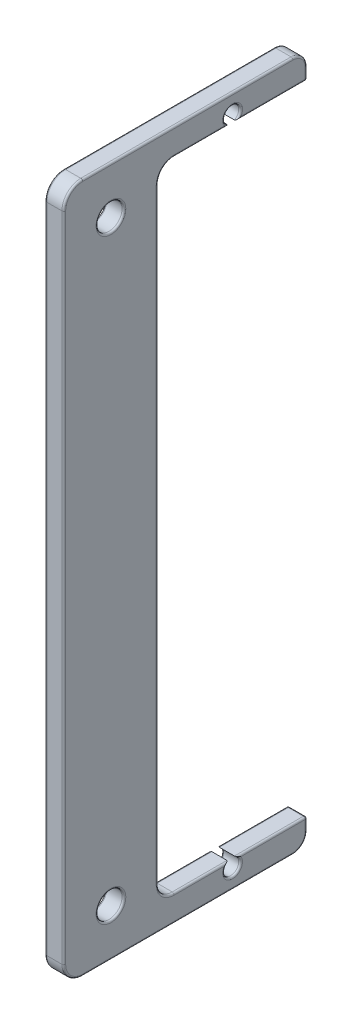
SolidWorks part; units mm, degrees
ref_plane "Front Plane" through (0, 0, 0) normal (0, 0, 1) x (1, 0, 0)
ref_plane "Top Plane" through (0, 0, 0) normal (0, 1, 0) x (1, 0, 0)
ref_plane "Right Plane" through (0, 0, 0) normal (1, 0, 0) x (0, 0, -1)
ref_plane "Plane1" through (102.035, 0, 0) normal (-1, 0, 0) x (0, -1, 0)
sketch "Sketch1" plane through (102.035, 0, 0) normal (-1, 0, 0) x (0, -1, 0)
  line L0 (-127.6, 102.4783) -> (7.6, 102.4783)
  line L2 (13.2, 122.4783) -> (-133.2, 122.4783)
  line L3 (-133.2, 122.4783) -> (-133.2, 70.8783)
  line L4 (-133.2, 70.8783) -> (-127.6, 70.8783)
  line L5 (-127.6, 70.8783) -> (-127.6, 102.4783)
  line L8 (13.2, 122.4783) -> (13.2, 70.8783)
  line L9 (13.2, 70.8783) -> (7.6, 70.8783)
  line L10 (7.6, 70.8783) -> (7.6, 102.4783)
  dimension "D1" = 5.6
  dimension "D2" = 5.6
  dimension "D3" = 51.6
  dimension "D4" = 20
  dimension "D7" = 146.4
extrude "Boss-Extrude1" add sketch "Sketch1" against normal blind 4
ref_plane "Plane2" through (0, 0, 86.4786) normal (0, 0, -1) x (-1, 0, 0)
sketch "Sketch6" plane through (106.035, 0, 0) normal (1, 0, 0) x (0, 0, -1)
  line L0 (-122.4783, 133.2) -> (-70.8783, 133.2) construction
  line L1 (-122.4783, -13.2) -> (-122.4783, 133.2) construction
  line L2 (-70.8783, 133.2) -> (-70.8783, 127.6) construction
  line L3 (-70.8783, -13.2) -> (-122.4783, -13.2) construction
  line L4 (-70.8783, -7.6) -> (-70.8783, -13.2) construction
  circle A0 centre (-86.6783, 129.1) radius 1.7
  circle A1 centre (-112.4783, 123.2) radius 2.75
  circle A2 centre (-112.4783, -3.2) radius 2.75
  circle A3 centre (-86.6783, -9.1) radius 1.7
  dimension "D1" = 3.4
  dimension "D2" = 5.5
  dimension "D3" = 10
  dimension "D5" = 15.8
  dimension "D6" = 4.1
  dimension "D7" = 4.1
  dimension "D8" = 15.8
  dimension "D9" = 10
  dimension "D10" = 10
  dimension "D4" = 10
extrude "Holes" cut sketch "Sketch6" against normal through all
fillet "Fillet1" radius 0.4 6 edges at (104.035, 127.6, 70.8783) (104.035, -7.6, 70.8783) (102.035, 123.2, 109.7283) (102.035, -3.2, 109.7283) (106.035, -3.2, 109.7283) (106.035, 123.2, 109.7283)
fillet "Fillet3" radius 3 2 edges at (104.035, 133.2, 70.8783) (104.035, -13.2, 70.8783)
fillet "Fillet5" radius 4 2 edges at (104.035, 133.2, 122.4783) (104.035, -13.2, 122.4783)
fillet "Fillet6" radius 3.4 2 edges at (104.035, -7.6, 102.4783) (104.035, 127.6, 102.4783)
fillet "Fillet7" radius 0.4 40 edges at (102.035, -12.0284, 121.3067) (102.035, -13.2, 96.1783) (102.035, -12.3213, 71.757) (102.035, -9.1, 70.8783) (102.035, -7.7172, 70.9954) (102.035, -7.6, 78.5783) (102.035, -10.8, 86.6783) (102.035, -7.6, 93.2783) (102.035, -6.6042, 101.4825) (102.035, 60, 102.4783) (102.035, 126.6042, 101.4825) (102.035, 127.6, 93.2783) (102.035, 130.8, 86.6783) (102.035, 127.6, 78.5783) (102.035, 127.7172, 70.9954) (102.035, 129.1, 70.8783) (102.035, 132.3213, 71.757) (102.035, 133.2, 96.1783) (102.035, 132.0284, 121.3067) (102.035, 60, 122.4783) (106.035, 60, 122.4783) (106.035, 132.0284, 121.3067) (106.035, 133.2, 96.1783) (106.035, 132.3213, 71.757) (106.035, 129.1, 70.8783) (106.035, 127.7172, 70.9954) (106.035, 127.6, 78.5783) (106.035, 130.8, 86.6783) (106.035, 127.6, 93.2783) (106.035, 126.6042, 101.4825) (106.035, 60, 102.4783) (106.035, -6.6042, 101.4825) (106.035, -7.6, 93.2783) (106.035, -10.8, 86.6783) (106.035, -7.6, 78.5783) (106.035, -7.7172, 70.9954) (106.035, -9.1, 70.8783) (106.035, -12.3213, 71.757) (106.035, -13.2, 96.1783) (106.035, -12.0284, 121.3067)
